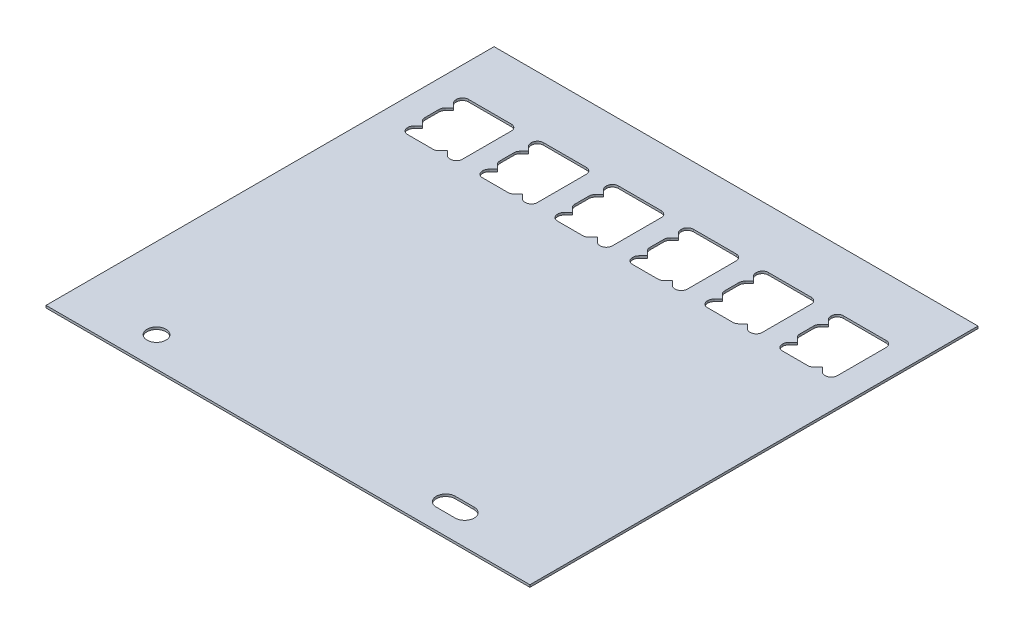
SolidWorks part; units mm, degrees
ref_plane "Front Plane" through (0, 0, 0) normal (0, 0, 1) x (1, 0, 0)
ref_plane "Top Plane" through (0, 0, 0) normal (0, 1, 0) x (1, 0, 0)
ref_plane "Right Plane" through (0, 0, 0) normal (1, 0, 0) x (0, 0, -1)
sketch "Sketch1" plane through (0, 0, 0) normal (0, 1, 0) x (1, 0, 0)
  line L1 (0, 0) -> (81, 0)
  line L2 (0, 0) -> (0, 75)
  line L3 (0, 75) -> (81, 75)
  line L4 (81, 0) -> (81, 75)
extrude "Boss-Extrude1" add sketch "Sketch1" against normal blind 0.381
sketch "Sketch2" plane through (0, 0, 0) normal (0, 1, 0) x (1, 0, 0)
  line L0 (0, 75) -> (0, 0) construction
  line L1 (0, 0) -> (81, 0) construction
  line L2 (61.915, 5) -> (65.085, 5) construction
  line L3 (61.915, 6.585) -> (65.085, 6.585)
  line L4 (61.915, 3.415) -> (65.085, 3.415)
  circle A0 centre (13.5, 5) radius 1.585
  arc A2 (61.915, 6.585) -> (61.915, 3.415) centre (61.915, 5) ccw
  arc A3 (65.085, 3.415) -> (65.085, 6.585) centre (65.085, 5) ccw
  point P10 (63.5, 5)
  line B0 (5.49, 55.02) -> (9.7558, 55.02)
  line B1 (12.5842, 55.02) -> (12.67, 55.02)
  line B2 (13.67, 56.02) -> (13.67, 64.22)
  line B3 (5.49, 65.22) -> (12.67, 65.22)
  line B4 (5.49, 62.72) -> (4.7829, 62.0129)
  line B5 (11.8771, 55.3129) -> (11.17, 56.02)
  line B6 (11.17, 56.02) -> (10.4629, 55.3129)
  line B7 (5.49, 57.52) -> (4.7829, 56.8129)
  line B8 (4.49, 64.22) -> (4.49, 64.1342)
  line B9 (5.49, 57.52) -> (4.7829, 58.2271)
  line B10 (5.49, 62.72) -> (4.7829, 63.4271)
  line B11 (4.49, 61.3058) -> (4.49, 58.9342)
  line B12 (4.49, 56.1058) -> (4.49, 56.02)
  arc B13 (12.67, 65.22) -> (13.67, 64.22) centre (12.67, 64.22) cw
  arc B14 (4.49, 64.22) -> (5.49, 65.22) centre (5.49, 64.22) cw
  arc B15 (4.49, 56.02) -> (5.49, 55.02) centre (5.49, 56.02) ccw
  arc B16 (13.67, 56.02) -> (12.67, 55.02) centre (12.67, 56.02) cw
  arc B17 (4.49, 61.3058) -> (4.7829, 62.0129) centre (5.49, 61.3058) cw
  arc B18 (4.7829, 58.2271) -> (4.49, 58.9342) centre (5.49, 58.9342) cw
  arc B19 (4.7829, 63.4271) -> (4.49, 64.1342) centre (5.49, 64.1342) cw
  arc B20 (4.49, 56.1058) -> (4.7829, 56.8129) centre (5.49, 56.1058) cw
  arc B21 (10.4629, 55.3129) -> (9.7558, 55.02) centre (9.7558, 56.02) cw
  arc B22 (12.5842, 55.02) -> (11.8771, 55.3129) centre (12.5842, 56.02) cw
  line B23 (18.04, 55.02) -> (22.3058, 55.02)
  line B24 (25.1342, 55.02) -> (25.22, 55.02)
  line B25 (26.22, 56.02) -> (26.22, 64.22)
  line B26 (18.04, 65.22) -> (25.22, 65.22)
  line B27 (18.04, 62.72) -> (17.3329, 62.0129)
  line B28 (24.4271, 55.3129) -> (23.72, 56.02)
  line B29 (23.72, 56.02) -> (23.0129, 55.3129)
  line B30 (18.04, 57.52) -> (17.3329, 56.8129)
  line B31 (17.04, 64.22) -> (17.04, 64.1342)
  line B32 (18.04, 57.52) -> (17.3329, 58.2271)
  line B33 (18.04, 62.72) -> (17.3329, 63.4271)
  line B34 (17.04, 61.3058) -> (17.04, 58.9342)
  line B35 (17.04, 56.1058) -> (17.04, 56.02)
  arc B36 (25.22, 65.22) -> (26.22, 64.22) centre (25.22, 64.22) cw
  arc B37 (17.04, 64.22) -> (18.04, 65.22) centre (18.04, 64.22) cw
  arc B38 (17.04, 56.02) -> (18.04, 55.02) centre (18.04, 56.02) ccw
  arc B39 (26.22, 56.02) -> (25.22, 55.02) centre (25.22, 56.02) cw
  arc B40 (17.04, 61.3058) -> (17.3329, 62.0129) centre (18.04, 61.3058) cw
  arc B41 (17.3329, 58.2271) -> (17.04, 58.9342) centre (18.04, 58.9342) cw
  arc B42 (17.3329, 63.4271) -> (17.04, 64.1342) centre (18.04, 64.1342) cw
  arc B43 (17.04, 56.1058) -> (17.3329, 56.8129) centre (18.04, 56.1058) cw
  arc B44 (23.0129, 55.3129) -> (22.3058, 55.02) centre (22.3058, 56.02) cw
  arc B45 (25.1342, 55.02) -> (24.4271, 55.3129) centre (25.1342, 56.02) cw
  line B46 (30.59, 55.02) -> (34.8558, 55.02)
  line B47 (37.6842, 55.02) -> (37.77, 55.02)
  line B48 (38.77, 56.02) -> (38.77, 64.22)
  line B49 (30.59, 65.22) -> (37.77, 65.22)
  line B50 (30.59, 62.72) -> (29.8829, 62.0129)
  line B51 (36.9771, 55.3129) -> (36.27, 56.02)
  line B52 (36.27, 56.02) -> (35.5629, 55.3129)
  line B53 (30.59, 57.52) -> (29.8829, 56.8129)
  line B54 (29.59, 64.22) -> (29.59, 64.1342)
  line B55 (30.59, 57.52) -> (29.8829, 58.2271)
  line B56 (30.59, 62.72) -> (29.8829, 63.4271)
  line B57 (29.59, 61.3058) -> (29.59, 58.9342)
  line B58 (29.59, 56.1058) -> (29.59, 56.02)
  arc B59 (37.77, 65.22) -> (38.77, 64.22) centre (37.77, 64.22) cw
  arc B60 (29.59, 64.22) -> (30.59, 65.22) centre (30.59, 64.22) cw
  arc B61 (29.59, 56.02) -> (30.59, 55.02) centre (30.59, 56.02) ccw
  arc B62 (38.77, 56.02) -> (37.77, 55.02) centre (37.77, 56.02) cw
  arc B63 (29.59, 61.3058) -> (29.8829, 62.0129) centre (30.59, 61.3058) cw
  arc B64 (29.8829, 58.2271) -> (29.59, 58.9342) centre (30.59, 58.9342) cw
  arc B65 (29.8829, 63.4271) -> (29.59, 64.1342) centre (30.59, 64.1342) cw
  arc B66 (29.59, 56.1058) -> (29.8829, 56.8129) centre (30.59, 56.1058) cw
  arc B67 (35.5629, 55.3129) -> (34.8558, 55.02) centre (34.8558, 56.02) cw
  arc B68 (37.6842, 55.02) -> (36.9771, 55.3129) centre (37.6842, 56.02) cw
  line B69 (43.14, 55.02) -> (47.4058, 55.02)
  line B70 (50.2342, 55.02) -> (50.32, 55.02)
  line B71 (51.32, 56.02) -> (51.32, 64.22)
  line B72 (43.14, 65.22) -> (50.32, 65.22)
  line B73 (43.14, 62.72) -> (42.4329, 62.0129)
  line B74 (49.5271, 55.3129) -> (48.82, 56.02)
  line B75 (48.82, 56.02) -> (48.1129, 55.3129)
  line B76 (43.14, 57.52) -> (42.4329, 56.8129)
  line B77 (42.14, 64.22) -> (42.14, 64.1342)
  line B78 (43.14, 57.52) -> (42.4329, 58.2271)
  line B79 (43.14, 62.72) -> (42.4329, 63.4271)
  line B80 (42.14, 61.3058) -> (42.14, 58.9342)
  line B81 (42.14, 56.1058) -> (42.14, 56.02)
  arc B82 (50.32, 65.22) -> (51.32, 64.22) centre (50.32, 64.22) cw
  arc B83 (42.14, 64.22) -> (43.14, 65.22) centre (43.14, 64.22) cw
  arc B84 (42.14, 56.02) -> (43.14, 55.02) centre (43.14, 56.02) ccw
  arc B85 (51.32, 56.02) -> (50.32, 55.02) centre (50.32, 56.02) cw
  arc B86 (42.14, 61.3058) -> (42.4329, 62.0129) centre (43.14, 61.3058) cw
  arc B87 (42.4329, 58.2271) -> (42.14, 58.9342) centre (43.14, 58.9342) cw
  arc B88 (42.4329, 63.4271) -> (42.14, 64.1342) centre (43.14, 64.1342) cw
  arc B89 (42.14, 56.1058) -> (42.4329, 56.8129) centre (43.14, 56.1058) cw
  arc B90 (48.1129, 55.3129) -> (47.4058, 55.02) centre (47.4058, 56.02) cw
  arc B91 (50.2342, 55.02) -> (49.5271, 55.3129) centre (50.2342, 56.02) cw
  line B92 (55.69, 55.02) -> (59.9558, 55.02)
  line B93 (62.7842, 55.02) -> (62.87, 55.02)
  line B94 (63.87, 56.02) -> (63.87, 64.22)
  line B95 (55.69, 65.22) -> (62.87, 65.22)
  line B96 (55.69, 62.72) -> (54.9829, 62.0129)
  line B97 (62.0771, 55.3129) -> (61.37, 56.02)
  line B98 (61.37, 56.02) -> (60.6629, 55.3129)
  line B99 (55.69, 57.52) -> (54.9829, 56.8129)
  line B100 (54.69, 64.22) -> (54.69, 64.1342)
  line B101 (55.69, 57.52) -> (54.9829, 58.2271)
  line B102 (55.69, 62.72) -> (54.9829, 63.4271)
  line B103 (54.69, 61.3058) -> (54.69, 58.9342)
  line B104 (54.69, 56.1058) -> (54.69, 56.02)
  arc B105 (62.87, 65.22) -> (63.87, 64.22) centre (62.87, 64.22) cw
  arc B106 (54.69, 64.22) -> (55.69, 65.22) centre (55.69, 64.22) cw
  arc B107 (54.69, 56.02) -> (55.69, 55.02) centre (55.69, 56.02) ccw
  arc B108 (63.87, 56.02) -> (62.87, 55.02) centre (62.87, 56.02) cw
  arc B109 (54.69, 61.3058) -> (54.9829, 62.0129) centre (55.69, 61.3058) cw
  arc B110 (54.9829, 58.2271) -> (54.69, 58.9342) centre (55.69, 58.9342) cw
  arc B111 (54.9829, 63.4271) -> (54.69, 64.1342) centre (55.69, 64.1342) cw
  arc B112 (54.69, 56.1058) -> (54.9829, 56.8129) centre (55.69, 56.1058) cw
  arc B113 (60.6629, 55.3129) -> (59.9558, 55.02) centre (59.9558, 56.02) cw
  arc B114 (62.7842, 55.02) -> (62.0771, 55.3129) centre (62.7842, 56.02) cw
  line B115 (68.24, 55.02) -> (72.5058, 55.02)
  line B116 (75.3342, 55.02) -> (75.42, 55.02)
  line B117 (76.42, 56.02) -> (76.42, 64.22)
  line B118 (68.24, 65.22) -> (75.42, 65.22)
  line B119 (68.24, 62.72) -> (67.5329, 62.0129)
  line B120 (74.6271, 55.3129) -> (73.92, 56.02)
  line B121 (73.92, 56.02) -> (73.2129, 55.3129)
  line B122 (68.24, 57.52) -> (67.5329, 56.8129)
  line B123 (67.24, 64.22) -> (67.24, 64.1342)
  line B124 (68.24, 57.52) -> (67.5329, 58.2271)
  line B125 (68.24, 62.72) -> (67.5329, 63.4271)
  line B126 (67.24, 61.3058) -> (67.24, 58.9342)
  line B127 (67.24, 56.1058) -> (67.24, 56.02)
  arc B128 (75.42, 65.22) -> (76.42, 64.22) centre (75.42, 64.22) cw
  arc B129 (67.24, 64.22) -> (68.24, 65.22) centre (68.24, 64.22) cw
  arc B130 (67.24, 56.02) -> (68.24, 55.02) centre (68.24, 56.02) ccw
  arc B131 (76.42, 56.02) -> (75.42, 55.02) centre (75.42, 56.02) cw
  arc B132 (67.24, 61.3058) -> (67.5329, 62.0129) centre (68.24, 61.3058) cw
  arc B133 (67.5329, 58.2271) -> (67.24, 58.9342) centre (68.24, 58.9342) cw
  arc B134 (67.5329, 63.4271) -> (67.24, 64.1342) centre (68.24, 64.1342) cw
  arc B135 (67.24, 56.1058) -> (67.5329, 56.8129) centre (68.24, 56.1058) cw
  arc B136 (73.2129, 55.3129) -> (72.5058, 55.02) centre (72.5058, 56.02) cw
  arc B137 (75.3342, 55.02) -> (74.6271, 55.3129) centre (75.3342, 56.02) cw
  dimension "D8" = 5
  dimension "D2" = 3.37
  dimension "D3" = 3.37
  dimension "D4" = 3.37
  dimension "D5" = 3.37
  dimension "D6" = 3.37
  dimension "D7" = 55.02
  dimension "D9" = 50
  dimension "D10" = 4.49
  dimension "D11" = 13.5
sketch_block_instance "Block1-1"
sketch_block "Block1" parameters "D4"=1, "D5"=1, "D6"=1, "D7"=1, "D8"=1, "D9"=1, "D10"=1, "D11"=1, "D12"=1, "D13"=1, "D1"=2.5, "D2"=2.5, "D3"=45
sketch_block_instance "Block1-4"
sketch_block_instance "Block1-5"
sketch_block_instance "Block1-6"
sketch_block_instance "Block1-7"
sketch_block_instance "Block1-8"
extrude "Cut-Extrude1" cut sketch "Sketch2" against normal through all
